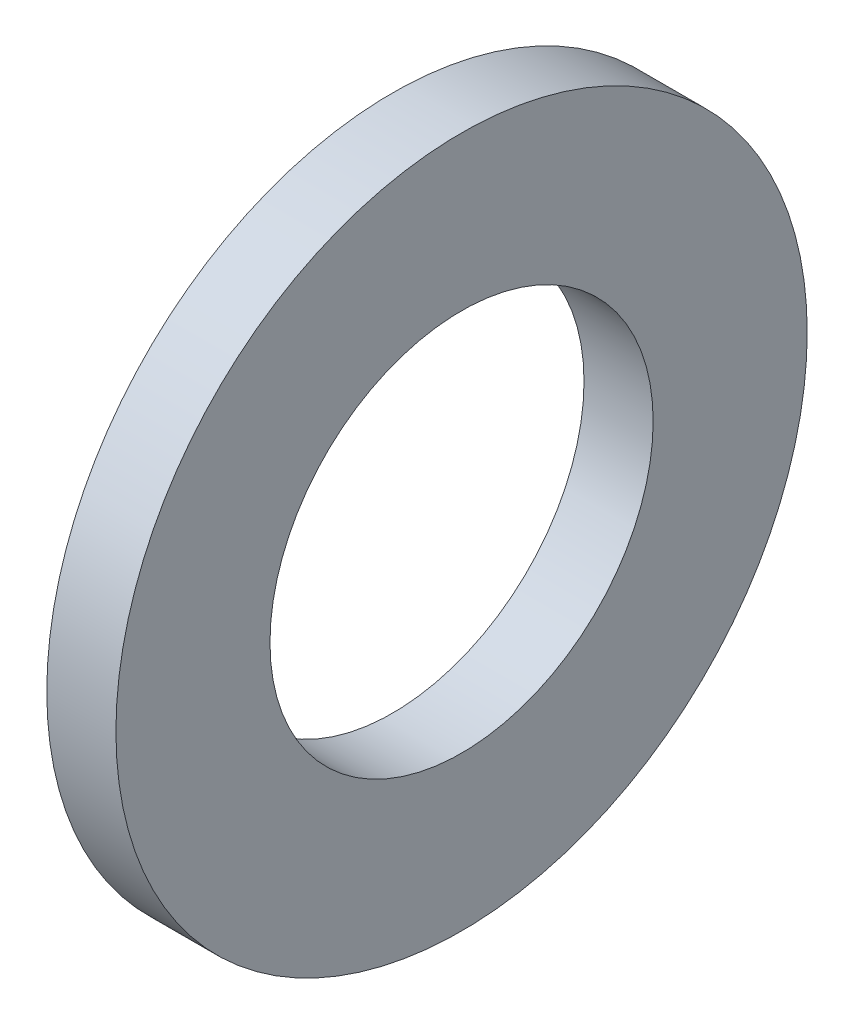
SolidWorks part; units mm, degrees
ref_plane "Plane1" through (0, 0, 0) normal (0, 0, 1) x (1, 0, 0)
ref_plane "Plane2" through (0, 0, 0) normal (0, 1, 0) x (1, 0, 0)
ref_plane "Plane3" through (0, 0, 0) normal (1, 0, 0) x (0, 0, -1)
sketch "Sketch1" plane through (0, 0, 0) normal (0, 0, 1) x (1, 0, 0)
  line L0 (-34.925, 0) -> (9.525, 0) construction
  line L1 (0, 7.76) -> (0, 14)
  line L2 (0, 14) -> (-2.8, 14)
  line L3 (-2.8, 14) -> (-2.8, 7.76)
  line L4 (-2.8, 7.76) -> (0, 7.76)
  dimension "Thickness" = 2.8
  dimension "Inside_dia" = 15.52
  dimension "Outside_dia" = 28
revolve "Base-Revolve" add sketch "Sketch1" angle 360 about L0
